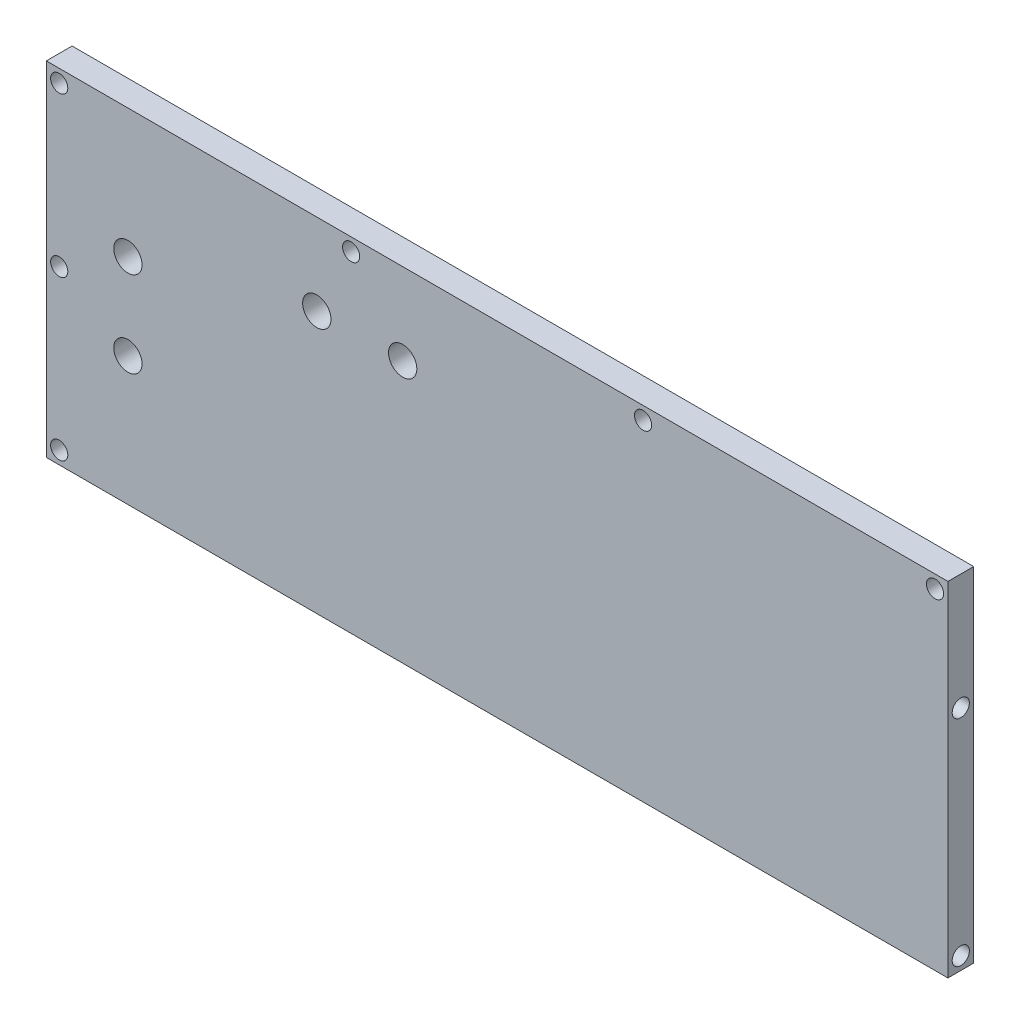
SolidWorks part; units mm, degrees
material "6061 合金"
ref_plane "前视" through (0, 0, 0) normal (0, 0, 1) x (1, 0, 0)
ref_plane "上视" through (0, 0, 0) normal (0, 1, 0) x (1, 0, 0)
ref_plane "右视" through (0, 0, 0) normal (1, 0, 0) x (0, 0, -1)
sketch "草图1" plane through (0, 0, 0) normal (0, 0, 1) x (1, 0, 0)
  line L0 (-105, -40) -> (105, -40)
  line L1 (-105, -40) -> (-105, 40)
  line L2 (105, -40) -> (105, 40)
  line L3 (-105, 40) -> (105, 40)
  line L4 (-105, -40) -> (105, 40) construction
  line L5 (105, -40) -> (-105, 40) construction
  point P1 (0, 0)
  dimension "D1" = 80
  dimension "D2" = 210
extrude "凸台-拉伸1" add sketch "草图1" along normal blind 6
sketch "草图2" plane through (0, 0, 6) normal (0, 0, 1) x (1, 0, 0)
  line L0 (-105, 40) -> (-105, -40) construction
  line L1 (105, 40) -> (-105, 40) construction
  circle A0 centre (-102, 0) radius 2
  circle A1 centre (-102, 37) radius 2
  circle A2 centre (-102, -37) radius 2
  circle A3 centre (-34, 37) radius 2
  circle A4 centre (34, 37) radius 2
  circle A5 centre (102, 37) radius 2
  dimension "D1" = 3
  dimension "D2" = 3
  dimension "D3" = 3
  dimension "D5" = 37
  dimension "D6" = 37
  dimension "D4" = 4
extrude "切除-拉伸1" cut sketch "草图2" against normal blind 6
sketch "草图3" plane through (105, 0, 0) normal (1, 0, 0) x (0, 0, -1)
  line L0 (-6, -40) -> (0, -40) construction
  circle A0 centre (-3, -37) radius 2
  circle A1 centre (-3, 13) radius 2
  dimension "D1" = 3
  dimension "D2" = 2
extrude "切除-拉伸2" cut sketch "草图3" against normal blind 20
sketch "草图4" plane through (0, 0, 6) normal (0, 0, 1) x (1, 0, 0)
  line L0 (0, 0) -> (-75.3385, 0) construction
  line L1 (-105, 40) -> (-105, -40) construction
  circle A0 centre (-86, 10) radius 3.3
  circle A1 centre (-86, -10) radius 3.3
  dimension "D1" = 6.6
  dimension "D3" = 19
  dimension "D2" = 10
extrude "切除-拉伸3" cut sketch "草图4" against normal blind 10
sketch "草图5" plane through (0, 0, 6) normal (0, 0, 1) x (1, 0, 0)
  line L0 (-32, 40) -> (-32, -8.7047) construction
  line L1 (105, 40) -> (-105, 40) construction
  line L2 (-105, 40) -> (-105, -40) construction
  circle A0 centre (-42, 21) radius 3.3
  circle A1 centre (-22, 21) radius 3.3
  dimension "D1" = 73
  dimension "D2" = 6.6
  dimension "D3" = 10
  dimension "D4" = 19
extrude "切除-拉伸4" cut sketch "草图5" against normal blind 10
